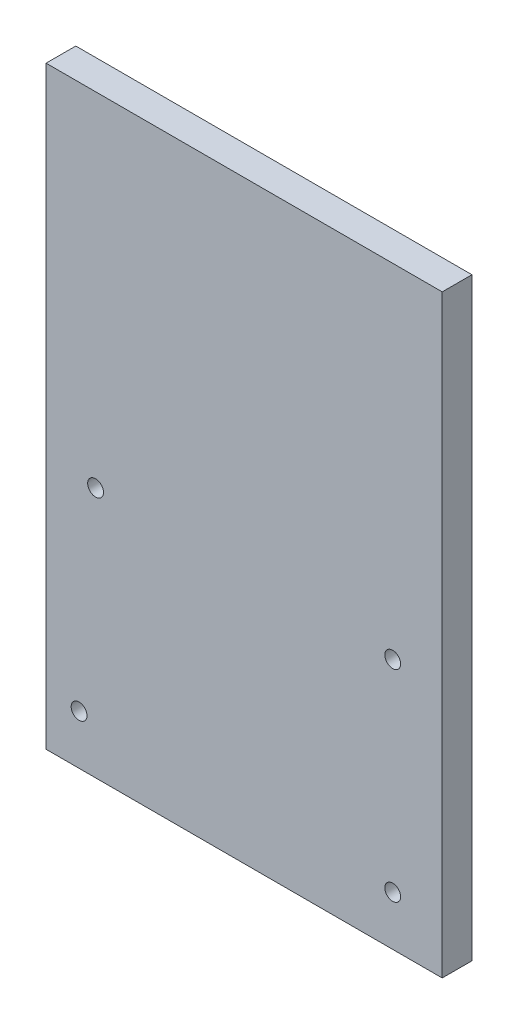
SolidWorks part; units mm, degrees
material "Roble"
ref_plane "Alzado" through (0, 0, 0) normal (0, 0, 1) x (1, 0, 0)
ref_plane "Planta" through (0, 0, 0) normal (0, 1, 0) x (1, 0, 0)
ref_plane "Vista lateral" through (0, 0, 0) normal (1, 0, 0) x (0, 0, -1)
sketch "Croquis1" plane through (0, 0, 0) normal (0, 0, 1) x (1, 0, 0)
  line L0 (0, 12.4932) -> (0, -12.3434) construction
  line L1 (-100, -150) -> (100, -150)
  line L2 (-100, -150) -> (-100, 150)
  line L3 (-100, 150) -> (100, 150)
  line L4 (100, -150) -> (100, 150)
  line L5 (-100, -150) -> (100, 150) construction
  line L6 (-100, 150) -> (100, -150) construction
  line L7 (-119.2766, -125) -> (112.4498, -125) construction
  line L8 (0, 128.6578) -> (0, -118.3138) construction
  line L9 (136.0798, -23.2) -> (-157.3895, -23.2) construction
  line L10 (-75.005, 112.5075) -> (-75.005, -93.4793) construction
  line L11 (75.005, 60.3384) -> (75.005, -93.4793) construction
  circle A0 centre (-75.005, -23.2) radius 4
  circle A1 centre (75.005, -23.2) radius 4
  circle A2 centre (75.005, -125) radius 4
  circle A3 centre (-83.3333, -125) radius 4
  point P0 (0, 0)
  point P18 (-75.005, -23.2)
  point P19 (75.005, -23.2)
  point P20 (75.005, -125)
  point P21 (-83.3333, -125)
  dimension "D7" = 8
  dimension "D1" = 200
  dimension "D2" = 300
  dimension "D3" = 25
  dimension "D4" = 101.8
  dimension "D5" = 75.005
  dimension "D6" = 75.005
extrude "Saliente-Extruir1" add sketch "Croquis1" along normal blind 15
